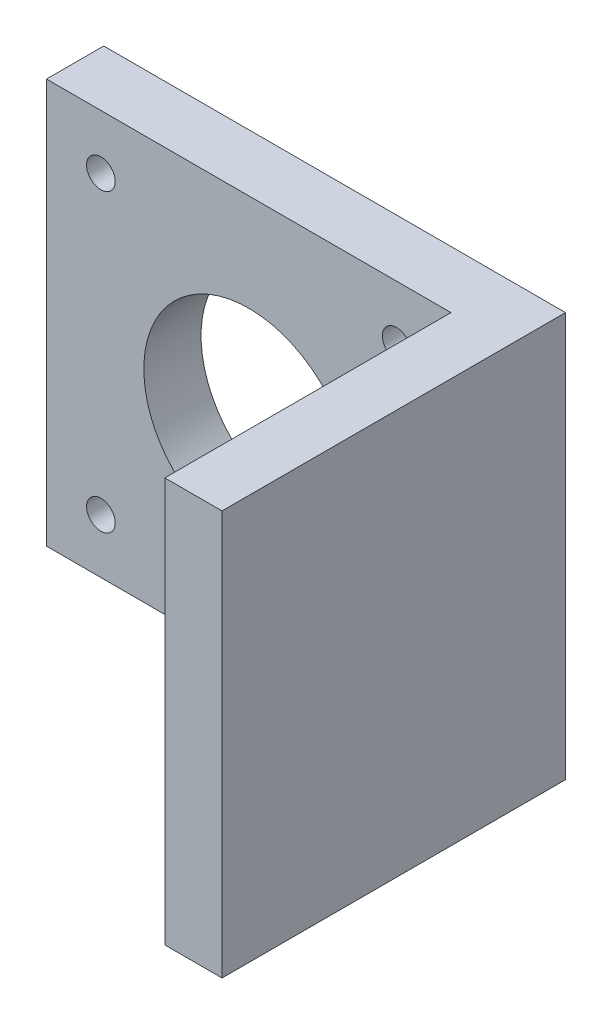
SolidWorks part; units mm, degrees
ref_plane "Front Plane" through (0, 0, 0) normal (0, 0, 1) x (1, 0, 0)
ref_plane "Top Plane" through (0, 0, 0) normal (0, 1, 0) x (1, 0, 0)
ref_plane "Right Plane" through (0, 0, 0) normal (1, 0, 0) x (0, 0, -1)
sketch "Sketch2" plane through (0, 0, 0) normal (0, 1, 0) x (1, 0, 0)
  line L0 (-42.4, 0) -> (0, 0)
  line L1 (0, 0) -> (0, -30)
  line L2 (-42.4, 0) -> (-42.4, 6)
  line L3 (-42.4, 6) -> (6, 6)
  line L4 (6, 6) -> (6, -30)
  line L5 (6, -30) -> (0, -30)
  dimension "D1" = 42.4
  dimension "D2" = 30
  dimension "D3" = 6
  dimension "D4" = 6
extrude "Boss-Extrude1" add sketch "Sketch2" along normal blind 42.4
sketch "Sketch3" plane through (0, 0, 0) normal (0, 0, 1) x (1, 0, 0)
  line L0 (-42.4, 42.4) -> (0, 0) construction
  line L2 (-36.7, 5.7) -> (-5.7, 5.7) construction
  line L3 (-36.7, 5.7) -> (-36.7, 36.7) construction
  line L4 (-36.7, 36.7) -> (-5.7, 36.7) construction
  line L5 (-5.7, 5.7) -> (-5.7, 36.7) construction
  line L6 (-36.7, 5.7) -> (-5.7, 36.7) construction
  line L7 (-36.7, 36.7) -> (-5.7, 5.7) construction
  circle A0 centre (-21.2, 21.2) radius 11
  circle A1 centre (-36.7, 36.7) radius 1.5
  circle A2 centre (-5.7, 36.7) radius 1.5
  circle A3 centre (-5.7, 5.7) radius 1.5
  circle A4 centre (-36.7, 5.7) radius 1.5
  dimension "D1" = 22
  dimension "D2" = 3
  dimension "D3" = 31
extrude "Cut-Extrude1" cut sketch "Sketch3" against normal through all
